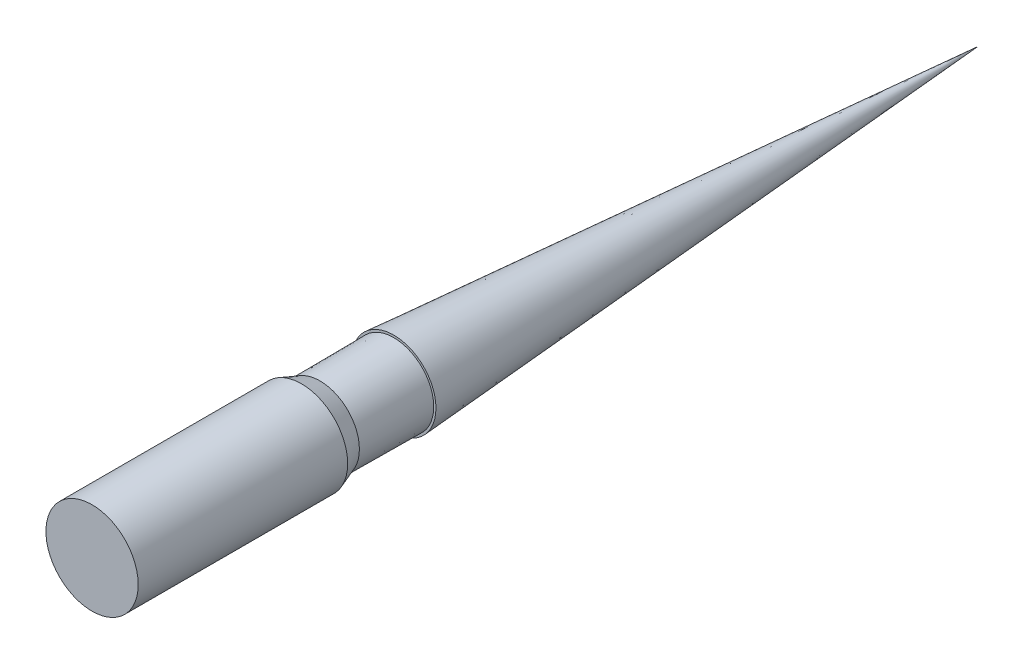
SolidWorks part; units mm, degrees
ref_plane "Front Plane" through (0, 0, 0) normal (0, 0, 1) x (1, 0, 0)
ref_plane "Top Plane" through (0, 0, 0) normal (0, 1, 0) x (1, 0, 0)
ref_plane "Right Plane" through (0, 0, 0) normal (1, 0, 0) x (0, 0, -1)
sketch "Sketch1" plane through (0, 0, 0) normal (0, 0, 1) x (1, 0, 0)
  circle A0 centre (0, 0) radius 15.875
extrude "Boss-Extrude1" add sketch "Sketch1" along normal blind 304.8
sketch "Sketch2" plane through (0, 0, 0) normal (1, 0, 0) x (0, 0, -1)
  line L0 (0, 0) -> (-200.9902, 14.5034)
  line L1 (-371.8105, 0) -> (37.0935, 0) construction
  line L2 (-200.9902, 14.5034) -> (-200.9902, 13.7414)
  line L3 (-200.9902, 13.7414) -> (-226.3902, 13.5636)
  line L4 (-226.3902, 13.5636) -> (-232.7402, 15.875)
  line L5 (0, 15.875) -> (-304.8, 15.875) construction
  line L6 (-232.7402, 15.875) -> (-232.7402, 31.694)
  line L7 (-232.7402, 31.694) -> (2.1943, 31.694)
  line L8 (0, 0) -> (0.9853, 0)
  line L9 (0.9853, 0) -> (2.1943, 31.694)
  point P12 (-226.6525, 12.2827)
  point P14 (0, 0)
  dimension "D1" = 13.7414
  dimension "D2" = 0.762
  dimension "D3" = 6.35
  dimension "D4" = 25.4
  dimension "D5" = 200.9902
  dimension "D7" = 13.5636
revolve "Cut-Revolve9" cut sketch "Sketch2" angle 360 about L1
